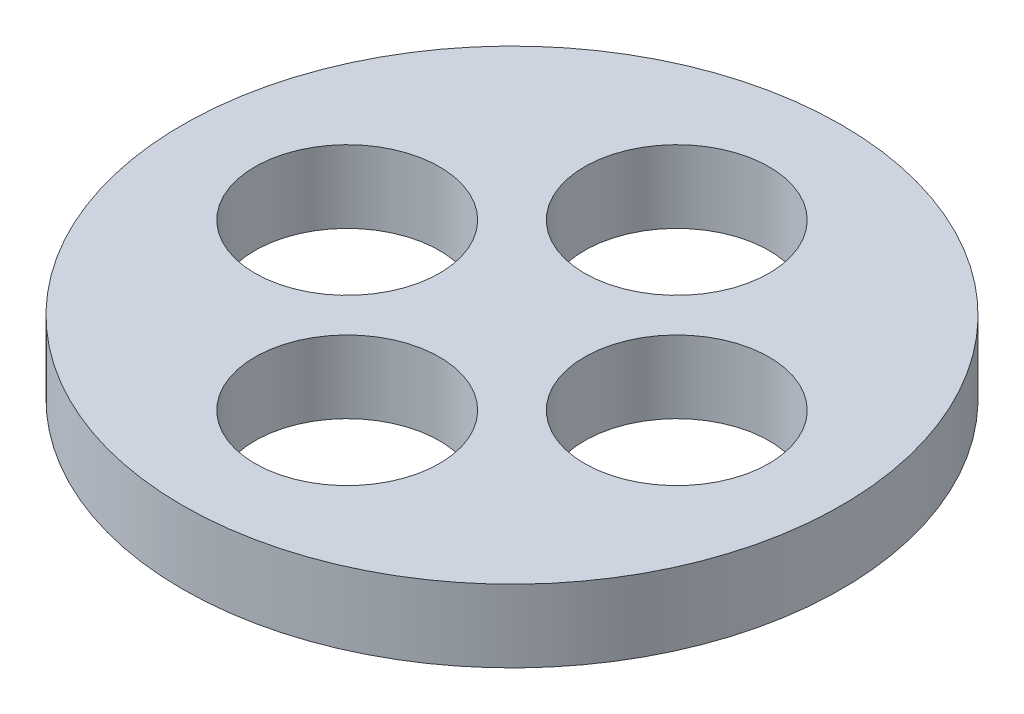
SolidWorks part; units mm, degrees
ref_plane "Front Plane" through (0, 0, 0) normal (0, 0, 1) x (1, 0, 0)
ref_plane "Top Plane" through (0, 0, 0) normal (0, 1, 0) x (1, 0, 0)
ref_plane "Right Plane" through (0, 0, 0) normal (1, 0, 0) x (0, 0, -1)
sketch "Sketch1" plane through (0, 0, 0) normal (0, 1, 0) x (1, 0, 0)
  circle A0 centre (0, 0) radius 25
  dimension "D1" = 50
extrude "Boss-Extrude1" add sketch "Sketch1" along normal blind 5.5
sketch "Sketch2" plane through (0, 5.5, 0) normal (0, 1, 0) x (1, 0, 0)
  line L0 (0, 0) -> (25, 0) construction
  line L1 (0, 0) -> (0, 25) construction
  line L2 (0, 0) -> (0, -25) construction
  line L3 (0, 0) -> (-25, 0) construction
  circle A0 centre (0, 0) radius 25 construction
  circle A1 centre (0, 12.5) radius 7
  circle A2 centre (12.5, 0) radius 7
  circle A3 centre (0, -12.5) radius 7
  circle A4 centre (-12.5, 0) radius 7
  dimension "D1" = 14
  dimension "D2" = 14
  dimension "D3" = 14
  dimension "D4" = 14
extrude "Cut-Extrude1" cut sketch "Sketch2" against normal blind 5.5
